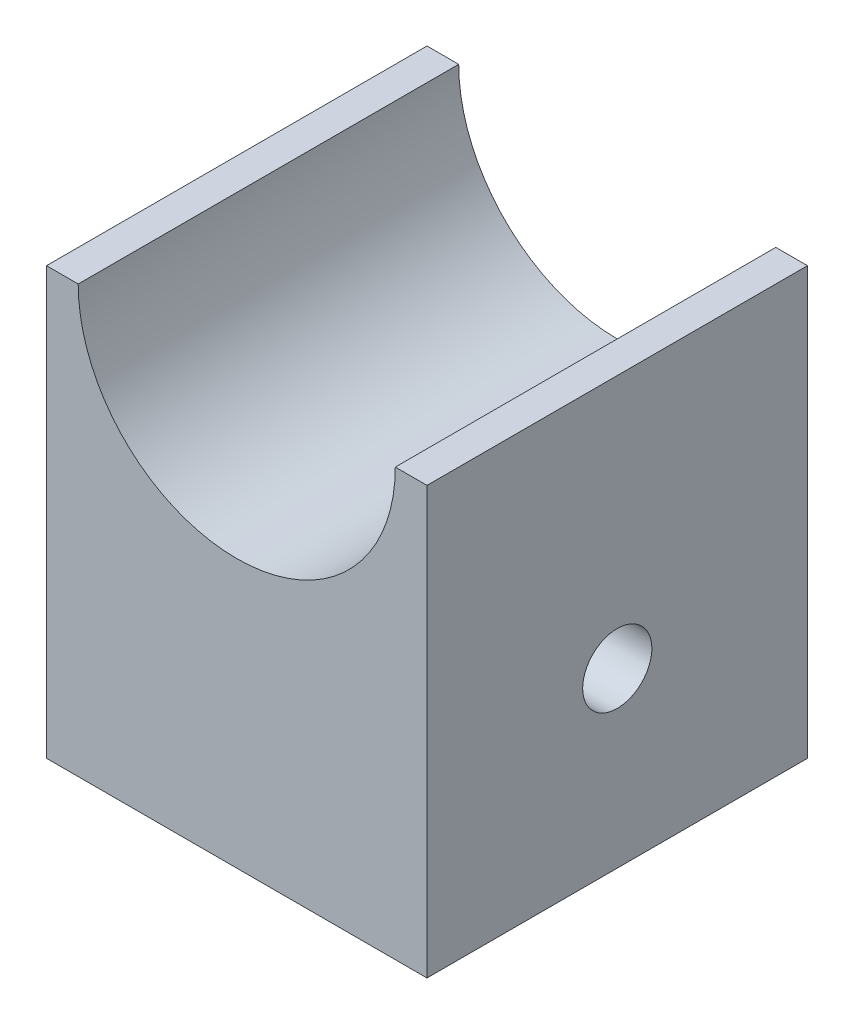
SolidWorks part; units mm, degrees
ref_plane "Front Plane" through (0, 0, 0) normal (0, 0, 1) x (1, 0, 0)
ref_plane "Top Plane" through (0, 0, 0) normal (0, 1, 0) x (1, 0, 0)
ref_plane "Right Plane" through (0, 0, 0) normal (1, 0, 0) x (0, 0, -1)
sketch "Sketch1" plane through (0, 0, 0) normal (0, 0, 1) x (1, 0, 0)
  line L1 (0, 0) -> (-33, 0)
  line L2 (0, 0) -> (0, 37)
  line L3 (0, 37) -> (-33, 37)
  line L4 (-33, 0) -> (-33, 37)
  dimension "D1" = 37
  dimension "D2" = 33
extrude "Boss-Extrude1" add sketch "Sketch1" along normal blind 33
sketch "Sketch2" plane through (0, 0, 33) normal (0, 0, 1) x (1, 0, 0)
  line L1 (0, 37) -> (-33, 37) construction
  circle A0 centre (-16.5, 37) radius 13.75
  point P3 (0, 0)
  point P4 (-16.5, 37)
  point P6 (-34.4715, 37)
  point P10 (0, 0)
  dimension "D3" = 27.5
  dimension "D1" = 0
extrude "Cut-Extrude1" cut sketch "Sketch2" against normal blind 33
sketch "Sketch3" plane through (-33, 0, 0) normal (-1, 0, 0) x (0, 0, 1)
  line L0 (33, 37) -> (33, 0) construction
  line L1 (0, 37) -> (0, 0) construction
  line L2 (33, 0) -> (0, 0) construction
  circle A0 centre (16.5, 15) radius 3
  dimension "D1" = 6
  dimension "D2" = 16.5
  dimension "D3" = 16.5
  dimension "D4" = 15
extrude "Cut-Extrude2" cut sketch "Sketch3" against normal blind 33
